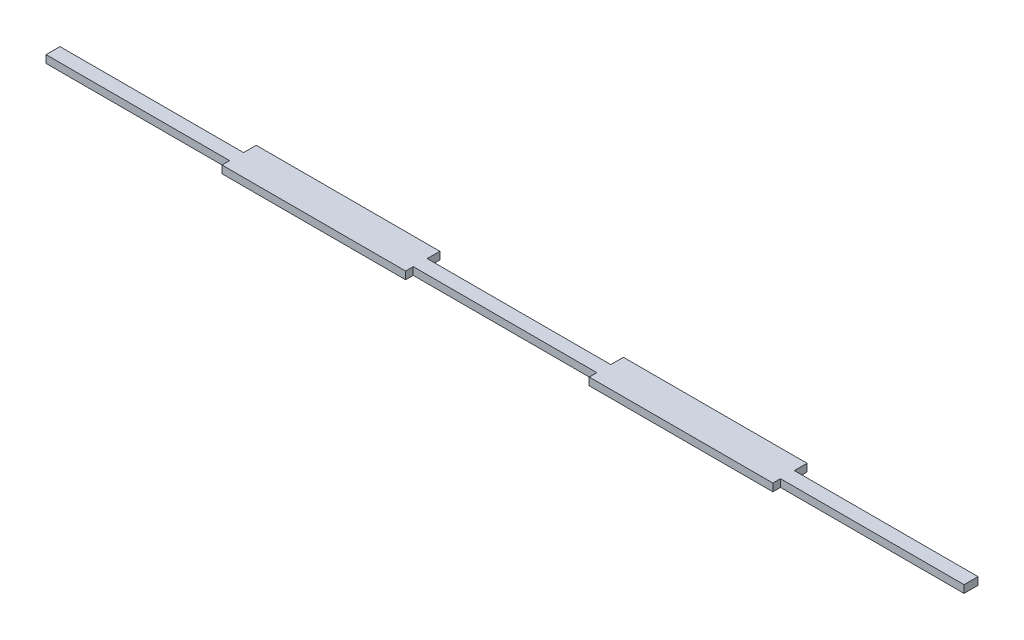
SolidWorks part; units mm, degrees
ref_plane "Front Plane" through (0, 0, 0) normal (0, 0, 1) x (1, 0, 0)
ref_plane "Top Plane" through (0, 0, 0) normal (0, 1, 0) x (1, 0, 0)
ref_plane "Right Plane" through (0, 0, 0) normal (1, 0, 0) x (0, 0, -1)
sketch "Sketch1" plane through (0, 0, 0) normal (0, 1, 0) x (1, 0, 0)
  line L2 (-181.15, 1.75) -> (-181.15, -3.75)
  line L3 (-108.69, -6.75) -> (-36.23, -6.75)
  line L4 (181.15, 1.75) -> (181.15, -3.75)
  line L5 (-181.15, 6.75) -> (181.15, -6.75) construction
  line L6 (-181.15, -6.75) -> (181.15, 6.75) construction
  line L7 (-108.69, 6.75) -> (-36.23, 6.75)
  line L9 (36.23, 6.75) -> (108.69, 6.75)
  line L11 (-108.69, 6.75) -> (-108.69, 1.75)
  line L12 (-108.69, 1.75) -> (-181.15, 1.75)
  line L13 (-36.23, 1.75) -> (36.23, 1.75)
  line L14 (-36.23, 6.75) -> (-36.23, 1.75)
  line L15 (36.23, 6.75) -> (36.23, 1.75)
  line L16 (108.69, 6.75) -> (108.69, 1.75)
  line L17 (108.69, 1.75) -> (181.15, 1.75)
  line L18 (-36.23, -3.75) -> (36.23, -3.75)
  line L19 (-181.15, -3.75) -> (-108.69, -3.75)
  line L20 (-108.69, -3.75) -> (-108.69, -6.75)
  line L21 (-36.23, -3.75) -> (-36.23, -6.75)
  line L22 (36.23, -3.75) -> (36.23, -6.75)
  line L23 (108.69, -3.75) -> (108.69, -6.75)
  line L24 (36.23, -6.75) -> (108.69, -6.75)
  line L25 (108.69, -3.75) -> (181.15, -3.75)
  point P0 (0, 0)
  dimension "D1" = 362.3
  dimension "D2" = 13.5
extrude "Boss-Extrude1" add sketch "Sketch1" along normal blind 3
